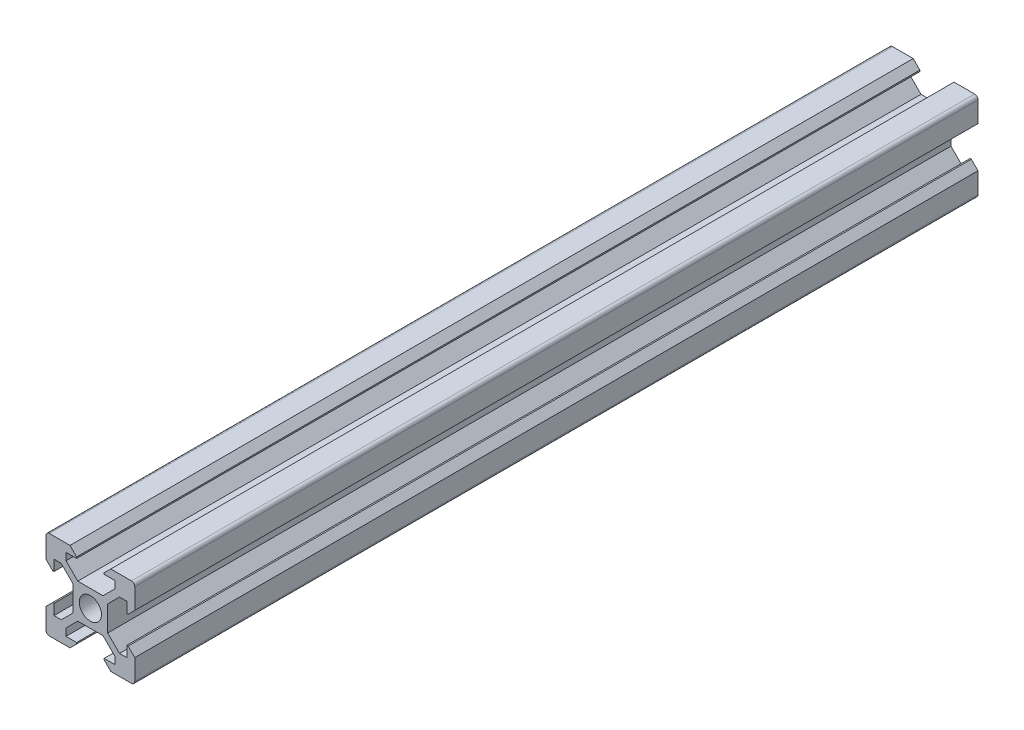
SolidWorks part; units mm, degrees
other "Markup1"
sketch "Sketch1" plane through (10, 10, 480) normal (0.5774, 0.5773, 0.5774) x (0.7071, 0, -0.7071)
ref_plane "Alzado" through (0, 0, 0) normal (0, 0, 1) x (1, 0, 0)
ref_plane "Planta" through (0, 0, 0) normal (0, 1, 0) x (1, 0, 0)
ref_plane "Vista lateral" through (0, 0, 0) normal (1, 0, 0) x (0, 0, -1)
sketch "Croquis1" plane through (0, 0, 0) normal (0, 0, 1) x (1, 0, 0)
  line L0 (-4.6, 10) -> (-3.1, 8.5)
  line L3 (-4.6, 10) -> (-9.25, 10)
  line L5 (-3.1, 8.5) -> (-3.1, 8.2)
  line L6 (-3.1, 8.2) -> (-5.5, 8.2)
  line L7 (-5.5, 8.2) -> (-5.5, 6.5607)
  line L8 (-5.5, 6.5607) -> (-2.84, 3.9007)
  line L9 (-2.84, 3.9007) -> (0, 3.9007)
  line L10 (0, 0) -> (-15.3499, 15.3499) construction
  line L11 (-3.9007, 2.84) -> (-3.9007, 0)
  line L12 (-6.5607, 5.5) -> (-3.9007, 2.84)
  line L13 (-8.2, 5.5) -> (-6.5607, 5.5)
  line L14 (-8.2, 3.1) -> (-8.2, 5.5)
  line L15 (-8.5, 3.1) -> (-8.2, 3.1)
  line L16 (-10, 4.6) -> (-10, 9.25)
  line L17 (-10, 4.6) -> (-8.5, 3.1)
  line L18 (10, 4.6) -> (8.5, 3.1)
  line L19 (10, 4.6) -> (10, 9.25)
  line L20 (8.5, 3.1) -> (8.2, 3.1)
  line L21 (8.2, 3.1) -> (8.2, 5.5)
  line L22 (8.2, 5.5) -> (6.5607, 5.5)
  line L23 (6.5607, 5.5) -> (3.9007, 2.84)
  line L24 (3.9007, 2.84) -> (3.9007, 0)
  line L25 (5.5, 6.5607) -> (2.84, 3.9007)
  line L26 (5.5, 8.2) -> (5.5, 6.5607)
  line L27 (3.1, 8.2) -> (5.5, 8.2)
  line L28 (3.1, 8.5) -> (3.1, 8.2)
  line L29 (4.6, 10) -> (9.25, 10)
  line L30 (4.6, 10) -> (3.1, 8.5)
  line L31 (2.84, 3.9007) -> (0, 3.9007)
  line L32 (4.6, -10) -> (3.1, -8.5)
  line L33 (4.6, -10) -> (9.25, -10)
  line L34 (3.1, -8.5) -> (3.1, -8.2)
  line L35 (3.1, -8.2) -> (5.5, -8.2)
  line L36 (5.5, -8.2) -> (5.5, -6.5607)
  line L37 (5.5, -6.5607) -> (2.84, -3.9007)
  line L38 (2.84, -3.9007) -> (0, -3.9007)
  line L39 (6.5607, -5.5) -> (3.9007, -2.84)
  line L40 (8.2, -5.5) -> (6.5607, -5.5)
  line L41 (8.2, -3.1) -> (8.2, -5.5)
  line L42 (8.5, -3.1) -> (8.2, -3.1)
  line L43 (10, -4.6) -> (10, -9.25)
  line L44 (10, -4.6) -> (8.5, -3.1)
  line L45 (3.9007, -2.84) -> (3.9007, 0)
  line L46 (-10, -4.6) -> (-8.5, -3.1)
  line L47 (-10, -4.6) -> (-10, -9.25)
  line L48 (-8.5, -3.1) -> (-8.2, -3.1)
  line L49 (-8.2, -3.1) -> (-8.2, -5.5)
  line L50 (-8.2, -5.5) -> (-6.5607, -5.5)
  line L51 (-6.5607, -5.5) -> (-3.9007, -2.84)
  line L52 (-3.9007, -2.84) -> (-3.9007, 0)
  line L53 (-5.5, -6.5607) -> (-2.84, -3.9007)
  line L54 (-5.5, -8.2) -> (-5.5, -6.5607)
  line L55 (-3.1, -8.2) -> (-5.5, -8.2)
  line L56 (-3.1, -8.5) -> (-3.1, -8.2)
  line L57 (-4.6, -10) -> (-9.25, -10)
  line L58 (-4.6, -10) -> (-3.1, -8.5)
  line L59 (-2.84, -3.9007) -> (0, -3.9007)
  circle A0 centre (0, 0) radius 2.5
  arc A1 (-9.25, 10) -> (-10, 9.25) centre (-9.25, 9.25) ccw
  arc A2 (10, 9.25) -> (9.25, 10) centre (9.25, 9.25) ccw
  arc A3 (9.25, -10) -> (10, -9.25) centre (9.25, -9.25) ccw
  arc A4 (-10, -9.25) -> (-9.25, -10) centre (-9.25, -9.25) ccw
  point P18 (-10, 10)
  point P37 (10, 10)
  point P55 (10, -10)
  point P73 (-10, -10)
  point P79 (0, 0)
  dimension "D1" = 5
  dimension "D5" = 0.75
  dimension "D2" = 10
  dimension "D3" = 10
  dimension "D4" = 4.6
  dimension "D6" = 5.5
  dimension "D7" = 135
  dimension "D8" = 0.75
  dimension "D9" = 225
  dimension "D10" = 2.84
  dimension "D11" = 1.8
  dimension "D12" = 3.1
  dimension "D13" = 4
extrude "Saliente-Extruir1" add sketch "Croquis1" along normal blind 190
